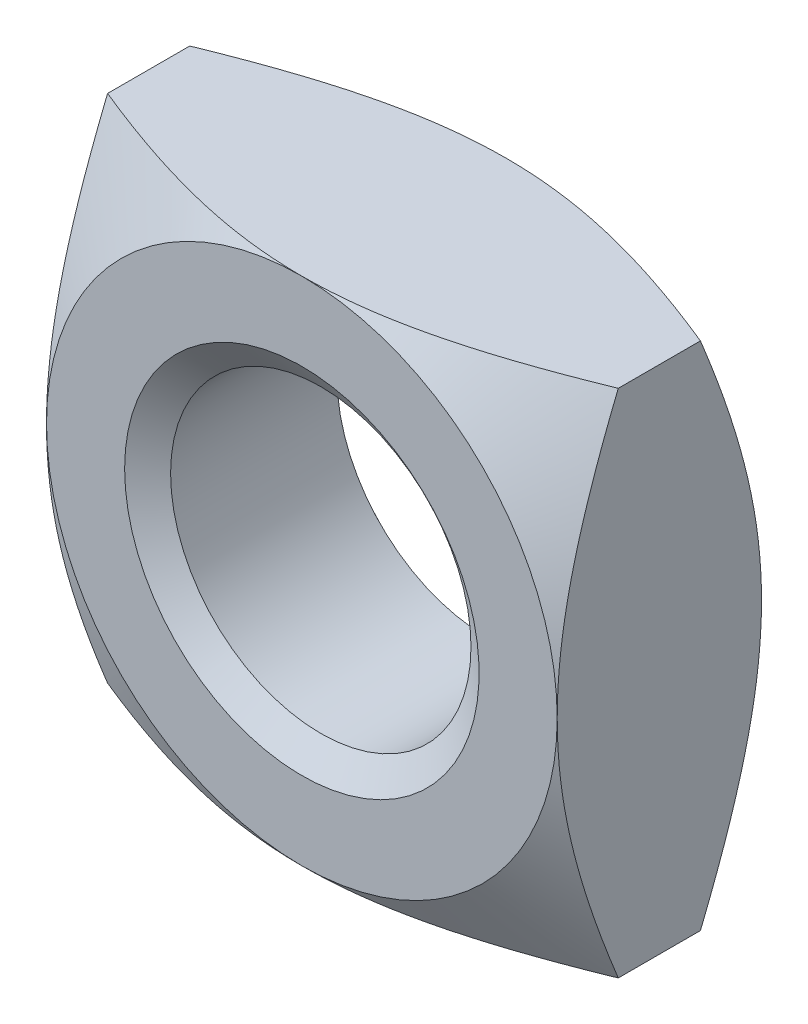
SolidWorks part; units mm, degrees
material "AISI 304"
ref_plane "Front Plane" through (0, 0, 0) normal (0, 0, 1) x (1, 0, 0)
ref_plane "Top Plane" through (0, 0, 0) normal (0, 1, 0) x (1, 0, 0)
ref_plane "Right Plane" through (0, 0, 0) normal (1, 0, 0) x (0, 0, -1)
sketch "Sketch1" plane through (0, 0, 0) normal (1, 0, 0) x (0, 0, -1)
  line L0 (2, 0) -> (-2, 0) construction
  line L1 (0, 0) -> (0, 3.9881) construction
  line L2 (0.4362, 5) -> (-0.4362, 5)
  line L3 (1.36, 3.4) -> (1.36, 2.36)
  line L4 (1.1079, 2) -> (-1.1079, 2)
  line L5 (-1.36, 3.4) -> (-1.36, 2.36)
  line L6 (0.4362, 5) -> (1.36, 3.4)
  line L7 (1.36, 2.36) -> (1.1079, 2)
  line L8 (-1.36, 2.36) -> (-1.1079, 2)
  line L9 (-0.4362, 5) -> (-1.36, 3.4)
  dimension "D1" = 4
  dimension "D2" = 10
  dimension "D3" = 4
  dimension "D4" = 2.72
  dimension "D5" = 35
  dimension "D6" = 30
  dimension "D7" = 6.8
  dimension "D8" = 4.72
revolve "Revolve1" add sketch "Sketch1" angle 360 about L0
cosmetic thread "Cosmetic Thread1" parameters "D1"=2.72, "D2"=4
sketch "Sketch2" plane through (0, 0, 0) normal (0, 0, 1) x (1, 0, 0)
  line L1 (-3.4, -3.4) -> (3.4, -3.4)
  line L2 (3.4, -3.4) -> (3.4, 3.4)
  line L3 (3.4, 3.4) -> (-3.4, 3.4)
  line L4 (-3.4, 3.4) -> (-3.4, -3.4)
  circle A0 centre (0, 0) radius 3.4 construction
  dimension "D1" = 6.8
extrude "Cut-Extrude1" cut sketch "Sketch2" against normal mid plane 2.72 flip side to cut
equation "\"D8@Sketch1\" = \"D3@Sketch1\" * 1.18"
equation "\"D7@Sketch1\"=\"D1@Sketch1\" * 1.7"
equation "\"D2@Sketch1\" = \"D1@Sketch1\" * 2.5"
equation "\"D4@Sketch1\" = \"D1@Sketch1\" * 0.68"
equation "\"D1@Cosmetic Thread1\" = \"D4@Sketch1\""
equation "\"D2@Cosmetic Thread1\" = \"D1@Sketch1\""
equation "\"D1@Sketch2\" = \"D7@Sketch1\""
equation "\"D1@Cut-Extrude1\" = \"D1@Cosmetic Thread1\""
